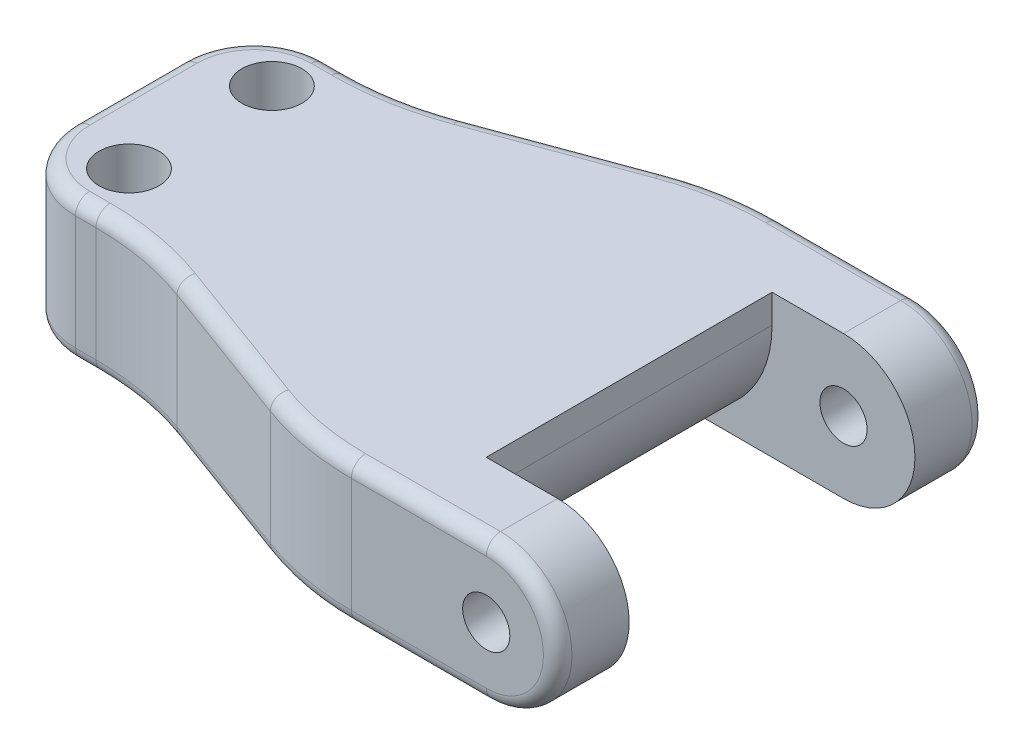
SolidWorks part; units mm, degrees
ref_plane "Front Plane" through (0, 0, 0) normal (0, 0, 1) x (1, 0, 0)
ref_plane "Top Plane" through (0, 0, 0) normal (0, 1, 0) x (1, 0, 0)
ref_plane "Right Plane" through (0, 0, 0) normal (1, 0, 0) x (0, 0, -1)
sketch "Sketch1" plane through (0, 0, 0) normal (0, 0, 1) x (1, 0, 0)
  line L0 (0, 5) -> (-40, 5)
  line L1 (-40, 5) -> (-40, -5)
  line L2 (-40, -5) -> (0, -5)
  arc A0 (0, -5) -> (0, 5) centre (0, 0) ccw
  circle A1 centre (0, 0) radius 1.65
  dimension "D1" = 10
  dimension "D2" = 3.3
  dimension "D3" = 45
extrude "Boss-Extrude1" add sketch "Sketch1" along normal mid plane 30
sketch "Sketch2" plane through (0, 0, 0) normal (0, 0, 1) x (1, 0, 0)
  line L1 (-40, -5) -> (0, -5) construction
  line L2 (0, 5) -> (-40, 5) construction
  line L3 (-5, 5) -> (0, 5)
  line L4 (0, -5) -> (-5, -5)
  line L5 (-5, -5) -> (-5, 5)
  arc A0 (0, -5) -> (0, 5) centre (0, 0) ccw
  arc A1 (0, -5) -> (0, 5) centre (0, 0) ccw construction
  circle A2 centre (0, 0) radius 5 construction
extrude "Cut-Extrude1" cut sketch "Sketch2" against normal mid plane 20
fillet "Fillet1" radius 8 1 edges at (-5, -5, 0)
sketch "Sketch3" plane through (0, -5, 0) normal (0, -1, 0) x (1, 0, 0)
  line L0 (-40, 0) -> (0, 0) construction
  line L1 (-40, 15) -> (-40, -15) construction
  line L2 (-40, 8.75) -> (-30, 8.75)
  line L3 (-30, 8.75) -> (-13, 15)
  line L4 (-40, 15) -> (0, 15) construction
  line L5 (-13, 15) -> (-40, 15)
  line L6 (-40, 15) -> (-40, 8.75)
  line L7 (-13, -15) -> (-40, -15)
  line L8 (-30, -8.75) -> (-13, -15)
  line L9 (-40, -8.75) -> (-30, -8.75)
  line L10 (-40, -15) -> (-40, -8.75)
  dimension "D1" = 10
  dimension "D2" = 17.5
extrude "Cut-Extrude2" cut sketch "Sketch3" against normal through all
sketch "Sketch4" plane through (0, 5, 0) normal (0, 1, 0) x (1, 0, 0)
  line L0 (-35, 8.75) -> (-35, -8.75) construction
  line L1 (-30, 8.75) -> (-40, 8.75) construction
  line L2 (-40, -8.75) -> (-30, -8.75) construction
  line L3 (-40, 0) -> (-30, 0) construction
  line L4 (-40, -8.75) -> (-40, 8.75) construction
  line L5 (-30, 0) -> (-30, 8.75) construction
  circle A0 centre (-35, 5) radius 2.1
  circle A1 centre (-35, -5) radius 2.1
  dimension "D1" = 4.2
  dimension "D2" = 10
extrude "Cut-Extrude3" cut sketch "Sketch4" against normal blind 3.5
fillet "Fillet2" radius 5 2 edges at (-40, 0, 8.75) (-40, 0, -8.75)
fillet "Fillet3" radius 20 4 edges at (-13, 0, -15) (-30, 0, -8.75) (-13, 0, 15) (-30, 0, 8.75)
fillet "Fillet5" radius 1 28 edges at (-40, 5, 0) (-38.5355, 5, -7.2855) (-34.28, 5, -8.75) (-30.0551, 5, -9.0595) (-21.5, 5, -11.875) (-12.9449, 5, -14.6905) (-4.72, 5, -15) (5, 0, -15) (-4.72, -5, -15) (-12.9449, -5, -14.6905) (-21.5, -5, -11.875) (-30.0551, -5, -9.0595) (-34.28, -5, -8.75) (-38.5355, -5, -7.2855) (-40, -5, 0) (-38.5355, -5, 7.2855) (-34.28, -5, 8.75) (-30.0551, -5, 9.0595) (-21.5, -5, 11.875) (-12.9449, -5, 14.6905) (-4.72, -5, 15) (5, 0, 15) (-4.72, 5, 15) (-12.9449, 5, 14.6905) (-21.5, 5, 11.875) (-30.0551, 5, 9.0595) (-34.28, 5, 8.75) (-38.5355, 5, 7.2855)
mirror "Mirror1" about plane through (0, 0, 0) normal (0, 1, 0) of "Cut-Extrude3"
